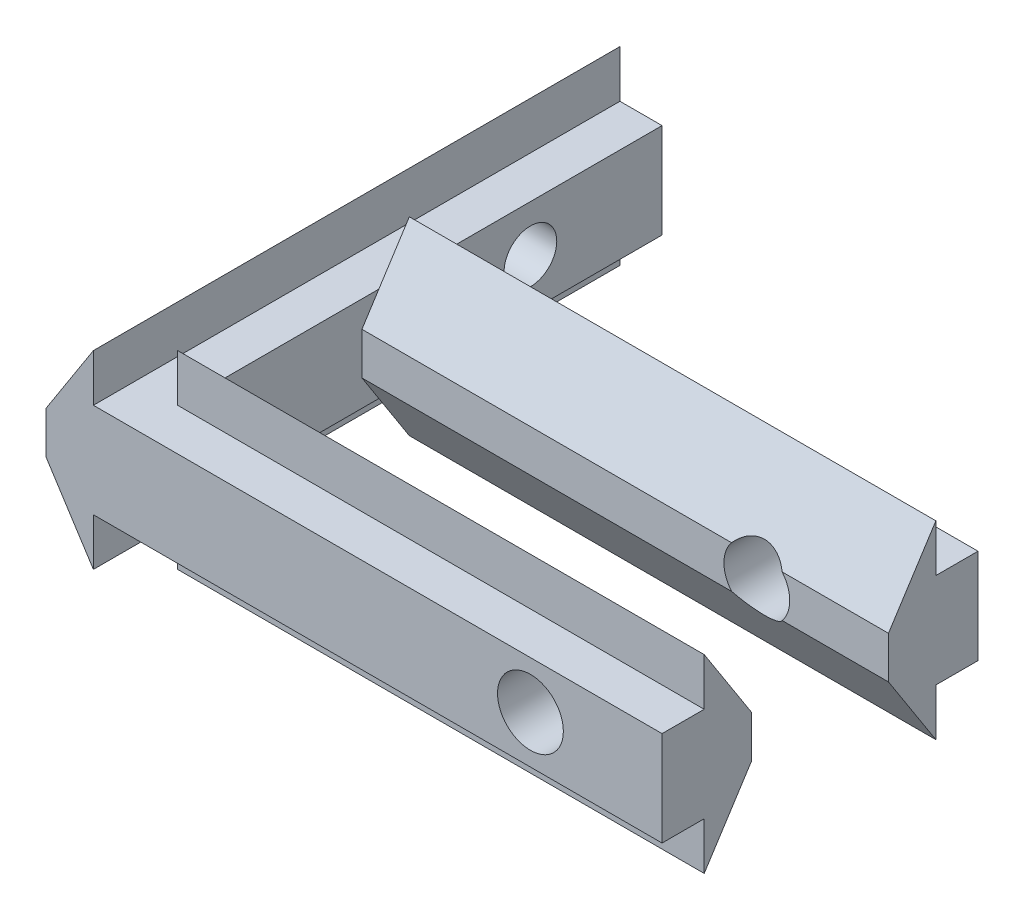
SolidWorks part; units mm, degrees
ref_plane "Plan de face" through (0, 0, 0) normal (0, 0, 1) x (1, 0, 0)
ref_plane "Plan de dessus" through (0, 0, 0) normal (0, 1, 0) x (1, 0, 0)
ref_plane "Plan de droite" through (0, 0, 0) normal (1, 0, 0) x (0, 0, -1)
sketch "ProfileRainureEsquisse" plane through (0, 0, 0) normal (0, 0, 1) x (1, 0, 0)
  line L0 (0, 0) -> (0, 1.6)
  line L1 (0, 1.6) -> (1.8, 4.4)
  line L2 (0, 0) -> (1.8, -2.8)
  line L3 (1.8, 4.4) -> (1.8, 2.6)
  line L4 (1.8, 2.6) -> (3.4, 2.6)
  line L5 (3.4, 2.6) -> (3.4, -1)
  line L6 (3.4, -1) -> (1.8, -1)
  line L7 (1.8, -1) -> (1.8, -2.8)
  dimension "D1" = 3.4
  dimension "D2" = 1.6
  dimension "D3" = 3.6
  dimension "D4" = 1.8
  dimension "D5" = 1.6
extrude "Boss.-Extru.1" add sketch "ProfileRainureEsquisse" along normal blind 20
sketch "Esquisse1" plane through (3.4, 0, 0) normal (1, 0, 0) x (0, 0, -1)
  line L0 (-20, -1) -> (-20, 2.6) construction
  circle A0 centre (-5, 0.8) radius 1
  point P2 (-20, 0.8)
  point P7 (-20, 0.8)
  point P10 (-20, 0.8)
  dimension "D1" = 2
  dimension "D2" = 15
extrude "Enlèv. mat.-Extru.1" cut sketch "Esquisse1" against normal through all
sketch "Esquisse2" plane through (3.4, 0, 0) normal (1, 0, 0) x (0, 0, -1)
  line L0 (-16.6, 0) -> (-16.6, 1.6)
  line L1 (-16.6, 1.6) -> (-18.4, 4.4)
  line L2 (-18.4, 4.4) -> (-18.4, 2.6)
  line L3 (-18.4, -2.8) -> (-16.6, 0)
  line L4 (-11.4, 1.6) -> (-11.4, 0)
  line L5 (-11.4, 0) -> (-9.6, -2.8)
  line L6 (-9.6, 4.4) -> (-9.6, 2.6)
  line L7 (-9.6, 4.4) -> (-11.4, 1.6)
  line L8 (-20, 2.6) -> (0, 2.6) construction
  line L9 (-18.4, 2.6) -> (-20, 2.6)
  line L10 (-20, 2.6) -> (0, 2.6) construction
  line L11 (-20, 2.6) -> (-20, -1)
  line L12 (-20, -1) -> (-18.4, -1)
  line L13 (-18.4, -1) -> (-18.4, -2.8)
  line L14 (-20, 4.4) -> (0, 4.4) construction
  line L15 (-9.6, 2.6) -> (-8, 2.6)
  line L16 (-20, -1) -> (0, -1) construction
  line L18 (-8, -1) -> (-9.6, -1)
  line L19 (-20, -1) -> (0, -1) construction
  line L20 (-9.6, -1) -> (-9.6, -2.8)
  line L21 (-20, -1) -> (-20, 2.6) construction
  line L23 (-8, 2.6) -> (-8, -1)
  dimension "D1" = 1.6
  dimension "D2" = 3.4
  dimension "D3" = 12
  dimension "D4" = 5.2
  dimension "D5" = 1.6
  dimension "D6" = 5.2
  dimension "D7" = 5.2
  dimension "D8" = 1.8
extrude "Boss.-Extru.2" add sketch "Esquisse2" along normal blind 20
sketch "Esquisse3" plane through (0, 0, 20) normal (0, 0, 1) x (1, 0, 0)
  line L0 (23.4, 2.6) -> (23.4, -1) construction
  circle A0 centre (18.4, 0.8) radius 1.25
  point P4 (23.4, 0.8)
  dimension "D1" = 2.5
  dimension "D2" = 5
extrude "Enlèv. mat.-Extru.2" cut sketch "Esquisse3" against normal through all
